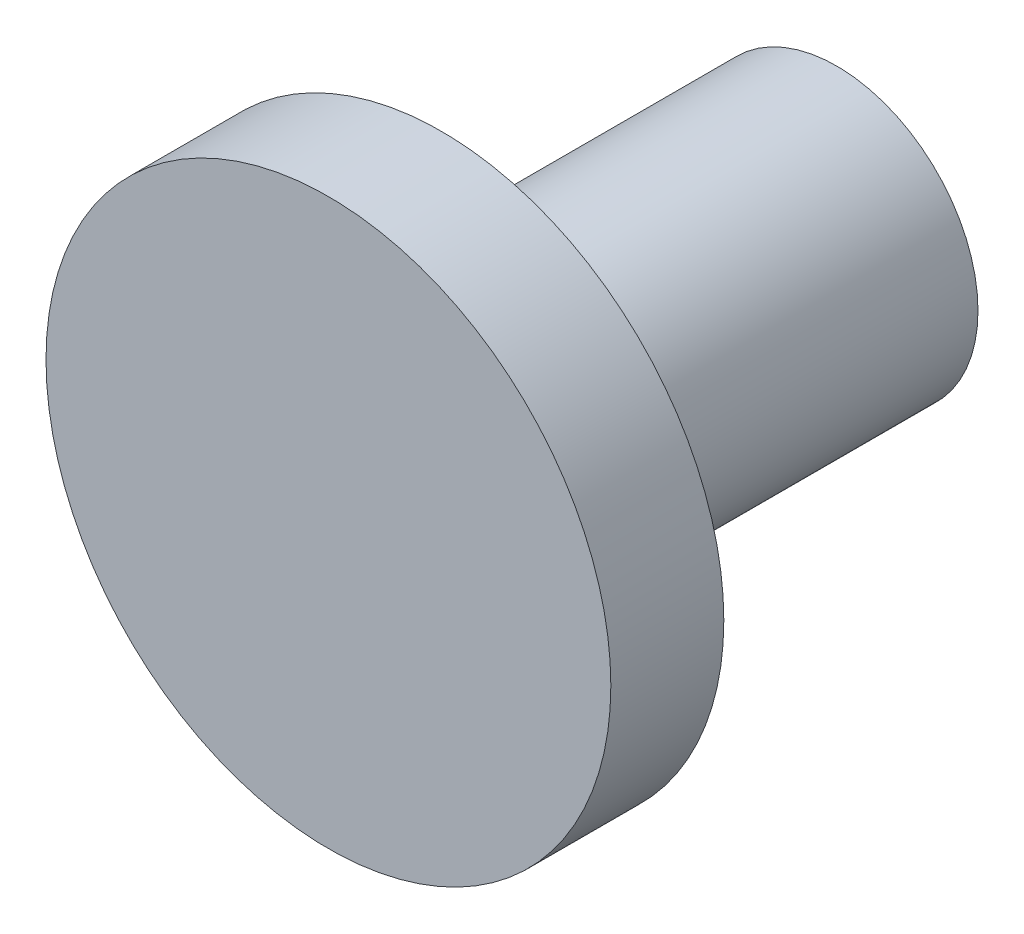
SolidWorks part; units mm, degrees
ref_plane "正面" through (0, 0, 0) normal (0, 0, 1) x (1, 0, 0)
ref_plane "平面" through (0, 0, 0) normal (0, 1, 0) x (1, 0, 0)
ref_plane "右側面" through (0, 0, 0) normal (1, 0, 0) x (0, 0, -1)
sketch "ｽｹｯﾁ1" plane through (0, 0, 0) normal (0, 0, 1) x (1, 0, 0)
  circle A0 centre (0, 0) radius 5
  dimension "D1" = 10
extrude "ﾎﾞｽ - 押し出し1" add sketch "ｽｹｯﾁ1" along normal blind 18
sketch "ｽｹｯﾁ2" plane through (0, 0, 18) normal (0, 0, 1) x (1, 0, 0)
  circle A0 centre (0, 0) radius 10
  dimension "D1" = 20
extrude "ﾎﾞｽ - 押し出し2" add sketch "ｽｹｯﾁ2" against normal blind 4
sketch "ｽｹｯﾁ3" plane through (0, 0, 0) normal (0, 0, -1) x (-1, 0, 0)
  circle A0 centre (0, 0) radius 1.6
  dimension "D1" = 3.2
extrude "ｶｯﾄ - 押し出し1" cut sketch "ｽｹｯﾁ3" against normal blind 12
